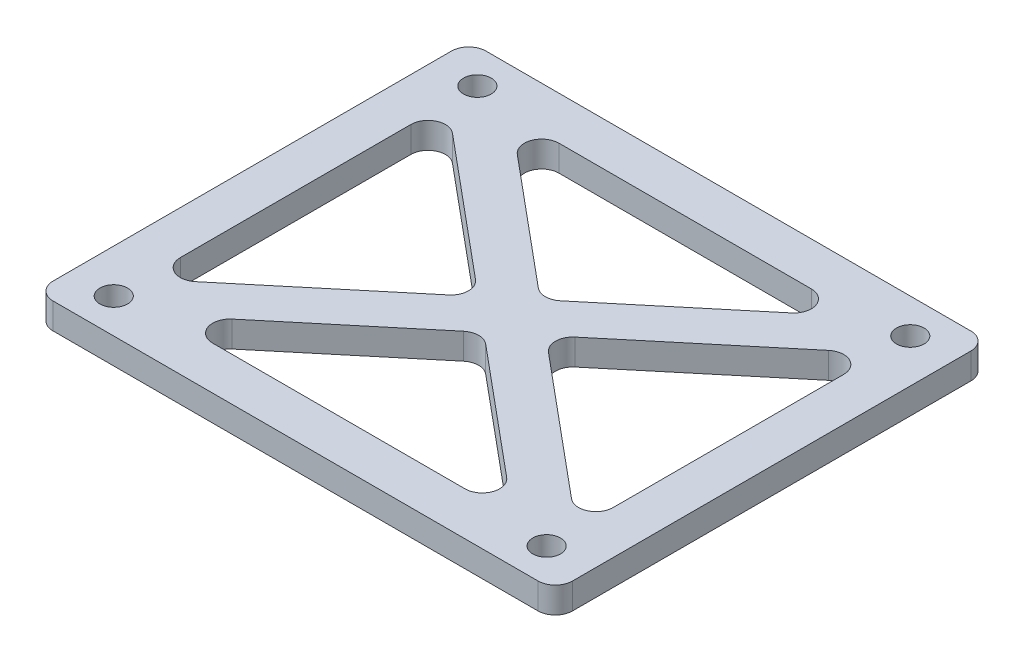
SolidWorks part; units mm, degrees
material "三聚氰胺甲醛树脂"
ref_plane "前视基准面" through (0, 0, 0) normal (0, 0, 1) x (1, 0, 0)
ref_plane "上视基准面" through (0, 0, 0) normal (0, 1, 0) x (1, 0, 0)
ref_plane "右视基准面" through (0, 0, 0) normal (1, 0, 0) x (0, 0, -1)
sketch "草图1" plane through (0, 0, 0) normal (0, 1, 0) x (1, 0, 0)
  line L0 (-25, 17.5791) -> (-3.9051, 0)
  line L1 (-30, 25) -> (30, 25)
  line L2 (-30, 25) -> (-30, -25)
  line L3 (-30, -25) -> (30, -25)
  line L4 (30, 25) -> (30, -25)
  line L5 (-30, 25) -> (30, -25) construction
  line L6 (-30, -25) -> (30, 25) construction
  line L8 (-25, 17.5791) -> (-25, -17.5791)
  line L10 (25, 17.5791) -> (25, -17.5791)
  line L11 (0, 0) -> (0, 3.3574) construction
  line L12 (0, 0) -> (4.8209, 0) construction
  line L13 (-3.9051, 0) -> (-25, -17.5791)
  line L14 (-20.0949, -20) -> (0, -3.2543)
  line L15 (0, -3.2543) -> (20.0949, -20)
  line L16 (25, -17.5791) -> (3.9051, 0)
  line L17 (3.9051, 0) -> (25, 17.5791)
  line L18 (20.0949, 20) -> (0, 3.2543)
  line L19 (0, 3.2543) -> (-20.0949, 20)
  line L20 (-20.0949, 20) -> (20.0949, 20)
  line L21 (-20.0949, -20) -> (20.0949, -20)
  circle A0 centre (-25, 21) radius 1.6
  circle A1 centre (25, 21) radius 1.6
  circle A2 centre (25, -21) radius 1.6
  circle A3 centre (-25, -21) radius 1.6
  point P0 (0, 0)
  point P6 (0, 0)
  point P23 (0, 0)
  dimension "D6" = 3.2
  dimension "D1" = 60
  dimension "D2" = 50
  dimension "D3" = 5
  dimension "D4" = 5
  dimension "D5" = 5
  dimension "D7" = 4
  dimension "D8" = 5
  dimension "D9" = 5
  dimension "D10" = 5
  dimension "D11" = 5
extrude "凸台-拉伸1" add sketch "草图1" along normal blind 3
fillet "圆角1" radius 2 4 edges at (30, 1.5, -25) (30, 1.5, 25) (-30, 1.5, 25) (-30, 1.5, -25)
fillet "圆角2" radius 2 12 edges at (-20.0949, 1.5, 20) (0, 1.5, 3.2543) (20.0949, 1.5, 20) (25, 1.5, 17.5791) (3.9051, 1.5, 0) (25, 1.5, -17.5791) (20.0949, 1.5, -20) (0, 1.5, -3.2543) (-20.0949, 1.5, -20) (-25, 1.5, -17.5791) (-3.9051, 1.5, 0) (-25, 1.5, 17.5791)
